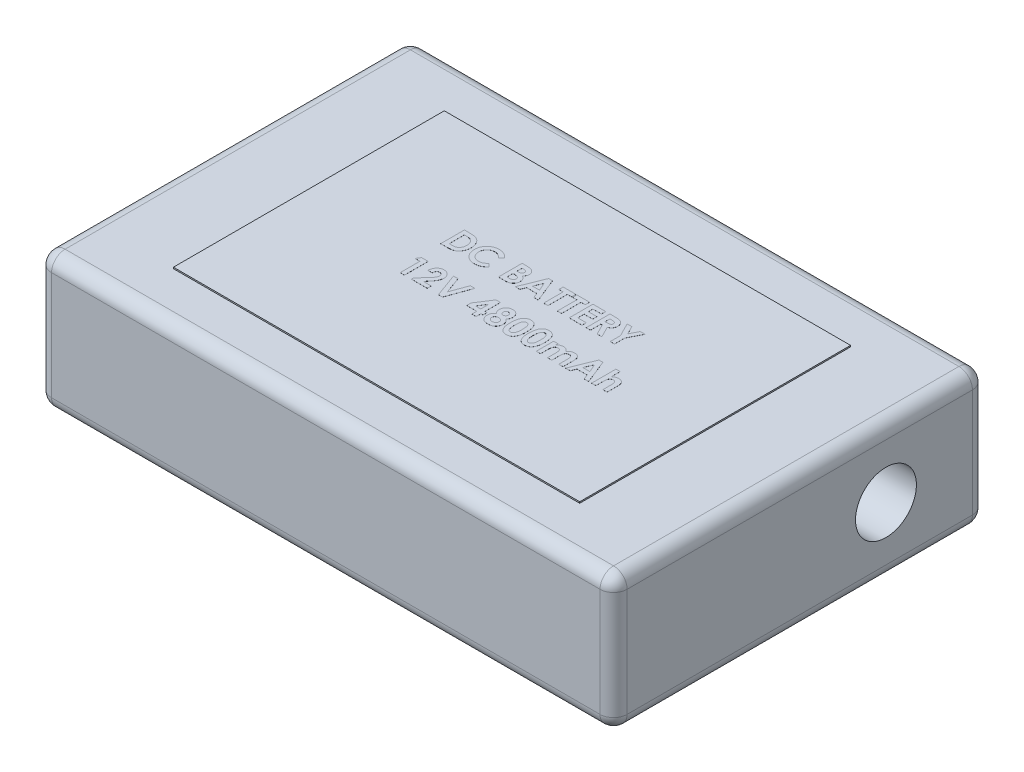
SolidWorks part; units mm, degrees
ref_plane "Front Plane" through (0, 0, 0) normal (0, 0, 1) x (1, 0, 0)
ref_plane "Top Plane" through (0, 0, 0) normal (0, 1, 0) x (1, 0, 0)
ref_plane "Right Plane" through (0, 0, 0) normal (1, 0, 0) x (0, 0, -1)
sketch "Sketch1" plane through (0, 0, 0) normal (0, 1, 0) x (1, 0, 0)
  line L1 (-42.5, -27.5) -> (42.5, -27.5)
  line L2 (-42.5, -27.5) -> (-42.5, 27.5)
  line L3 (-42.5, 27.5) -> (42.5, 27.5)
  line L4 (42.5, -27.5) -> (42.5, 27.5)
  line L5 (-42.5, -27.5) -> (42.5, 27.5) construction
  line L6 (-42.5, 27.5) -> (42.5, -27.5) construction
  point P0 (0, 0)
  dimension "D1" = 55
  dimension "D2" = 85
extrude "Boss-Extrude1" add sketch "Sketch1" along normal blind 20
fillet "Fillet1" radius 2 12 edges at (0, 20, 27.5) (-42.5, 20, 0) (0, 20, -27.5) (42.5, 20, 0) (0, 0, -27.5) (-42.5, 0, 0) (0, 0, 27.5) (42.5, 0, 0) (42.5, 10, -27.5) (-42.5, 10, -27.5) (-42.5, 10, 27.5) (42.5, 10, 27.5)
sketch "Sketch2" plane through (0, 20, 0) normal (0, 1, 0) x (1, 0, 0)
  line L1 (30, -20) -> (-30, -20)
  line L2 (30, -20) -> (30, 20)
  line L3 (30, 20) -> (-30, 20)
  line L4 (-30, -20) -> (-30, 20)
  line L5 (30, -20) -> (-30, 20) construction
  line L6 (30, 20) -> (-30, -20) construction
  point P0 (0, 0)
  dimension "D1" = 40
  dimension "D2" = 60
extrude "Boss-Extrude2" add sketch "Sketch2" along normal blind 0.2 separate body
sketch "Sketch3" plane through (0, 20.2, 0) normal (0, 1, 0) x (1, 0, 0)
  text T0 "<b>DC BATTERY</b>\r\n<b>12V 4800mAh</b>"
extrude "Boss-Extrude3" add sketch "Sketch3" along normal blind 0.01 separate body
sketch "Sketch4" plane through (42.5, 0, 0) normal (1, 0, 0) x (0, 0, -1)
  line L0 (12.7292, 18) -> (12.7292, 2) construction
  line L3 (25.5, 18) -> (-25.5, 18) construction
  line L4 (-25.5, 2) -> (25.5, 2) construction
  circle A0 centre (12.7292, 10) radius 4.5
  dimension "D1" = 9
extrude "Cut-Extrude1" cut sketch "Sketch4" against normal blind 20
